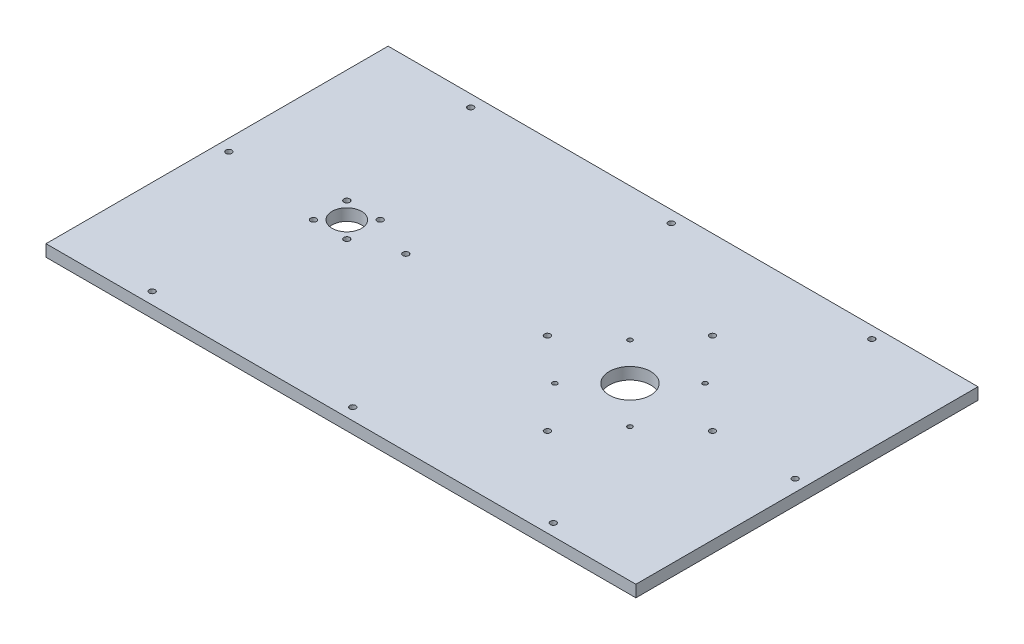
SolidWorks part; units mm, degrees
ref_plane "Front Plane" through (0, 0, 0) normal (0, 0, 1) x (1, 0, 0)
ref_plane "Top Plane" through (0, 0, 0) normal (0, 1, 0) x (1, 0, 0)
ref_plane "Right Plane" through (0, 0, 0) normal (1, 0, 0) x (0, 0, -1)
sketch "Sketch1" plane through (0, 0, 0) normal (0, 1, 0) x (1, 0, 0)
  line L0 (-90, 280.1918) -> (-90, -255.2259) construction
  line L1 (-250, -145) -> (250, -145)
  line L2 (-250, -145) -> (-250, 145)
  line L3 (-250, 145) -> (250, 145)
  line L4 (250, -145) -> (250, 145)
  line L5 (-250, -145) -> (250, 145) construction
  line L6 (-250, 145) -> (250, -145) construction
  line L7 (-240, -135) -> (240, -135) construction
  line L8 (-240, -135) -> (-240, 135) construction
  line L9 (-240, 135) -> (240, 135) construction
  line L10 (240, -135) -> (240, 135) construction
  line L11 (-240, -135) -> (240, 135) construction
  line L12 (-240, 135) -> (240, -135) construction
  line L13 (-317.3233, 0) -> (323.4582, 0) construction
  line L14 (-140, 0) -> (-113.6049, 26.3951) construction
  line L15 (100, 0) -> (168.2356, 68.2356) construction
  circle A0 centre (-240, 0) radius 2.5
  circle A1 centre (-90, 0) radius 2.5
  circle A2 centre (-170, -135) radius 2.5
  circle A3 centre (-170, 135) radius 2.5
  circle A4 centre (170, 135) radius 2.5
  circle A5 centre (240, 0) radius 2.5
  circle A6 centre (170, -135) radius 2.5
  circle A7 centre (0, 135) radius 2.5
  circle A8 centre (0, -135) radius 2.5
  circle A9 centre (100, 0) radius 17.5
  circle A10 centre (-140, 0) radius 12.5
  circle A11 centre (-140, 0) radius 20 construction
  circle A12 centre (-125.8579, 14.1421) radius 2.5
  circle A13 centre (100, 0) radius 45 construction
  circle A14 centre (100, 0) radius 70 construction
  circle A15 centre (-125.8579, -14.1421) radius 2.5
  circle A16 centre (-154.1421, -14.1421) radius 2.5
  circle A17 centre (-154.1421, 14.1421) radius 2.5
  circle A18 centre (170, 0) radius 2.5
  circle A19 centre (131.8198, 31.8198) radius 2
  circle A20 centre (100, -70) radius 2.5
  circle A21 centre (30, 0) radius 2.5
  circle A23 centre (100, 70) radius 2.5
  circle A24 centre (131.8198, -31.8198) radius 2
  circle A25 centre (68.1802, -31.8198) radius 2
  circle A26 centre (68.1802, 31.8198) radius 2
  point P0 (0, 0)
  point P6 (0, 0)
  point P13 (-90, 12.4829)
  point P51 (-120, 0)
  point P54 (-140, 0)
  point P68 (0, 0)
  point P69 (100, 0)
  point P70 (50, 0)
  point P76 (0, 0)
  point P78 (100, 0)
  point P79 (50, 0)
  dimension "D7" = 5
  dimension "D8" = 5
  dimension "D9" = 5
  dimension "D10" = 5
  dimension "D11" = 5
  dimension "D12" = 5
  dimension "D13" = 5
  dimension "D14" = 5
  dimension "D15" = 5
  dimension "D22" = 90
  dimension "D23" = 25
  dimension "D25" = 40
  dimension "D26" = 45
  dimension "D27" = 5
  dimension "D29" = 35
  dimension "D30" = 240
  dimension "D31" = 4
  dimension "D32" = 45
  dimension "D28" = 140
  dimension "D33" = 4
  dimension "D34" = 5
  dimension "D1" = 290
  dimension "D2" = 500
  dimension "D3" = 10
  dimension "D4" = 10
  dimension "D5" = 160
  dimension "D6" = 145
  dimension "D16" = 80
  dimension "D17" = 80
  dimension "D18" = 80
  dimension "D19" = 80
  dimension "D20" = 250
  dimension "D21" = 250
  dimension "D24" = 150
  dimension "D37" = 4
  dimension "D36" = 4
extrude "Boss-Extrude1" add sketch "Sketch1" along normal blind 10
